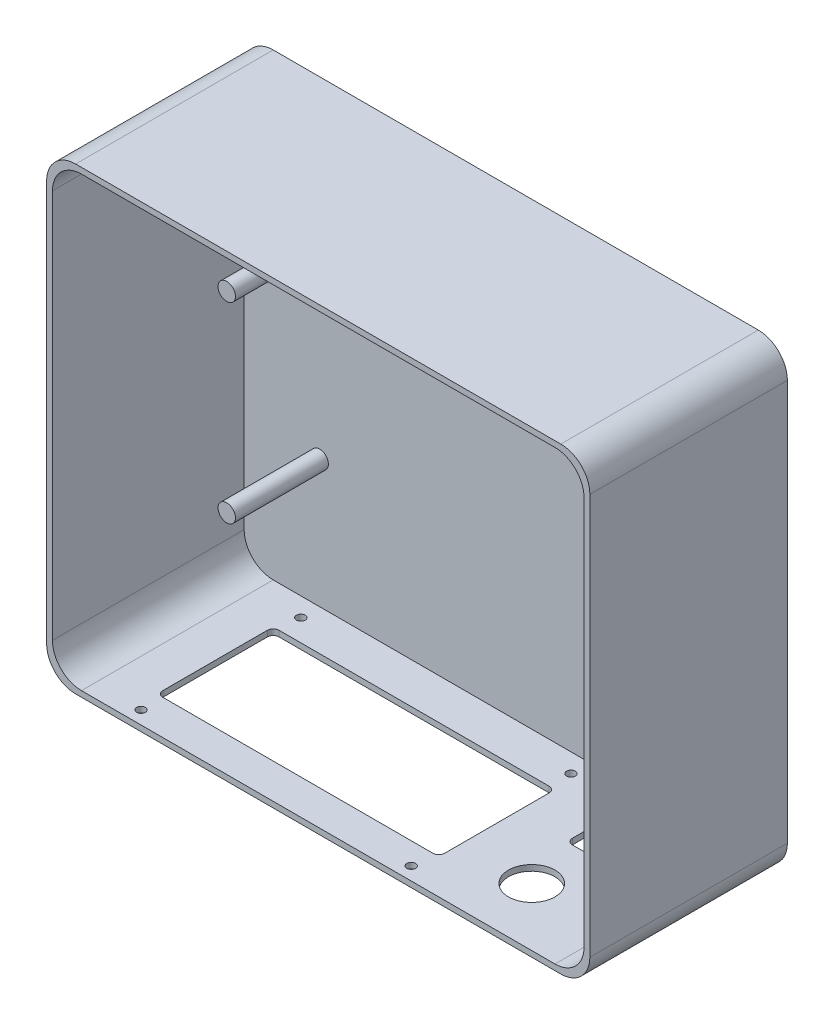
SolidWorks part; units mm, degrees
ref_plane "Front Plane" through (0, 0, 0) normal (0, 0, 1) x (1, 0, 0)
ref_plane "Top Plane" through (0, 0, 0) normal (0, 1, 0) x (1, 0, 0)
ref_plane "Right Plane" through (0, 0, 0) normal (1, 0, 0) x (0, 0, -1)
sketch "Sketch1" plane through (0, 0, 0) normal (0, 0, 1) x (1, 0, 0)
  line L1 (-93.5, 79) -> (93.5, 79)
  line L2 (-93.5, 79) -> (-93.5, -79)
  line L3 (-93.5, -79) -> (93.5, -79)
  line L4 (93.5, 79) -> (93.5, -79)
  line L5 (-93.5, 79) -> (93.5, -79) construction
  line L6 (-93.5, -79) -> (93.5, 79) construction
  line L7 (-91.5, 77) -> (91.5, 77)
  line L8 (-91.5, 77) -> (-91.5, -77)
  line L9 (-91.5, -77) -> (91.5, -77)
  line L10 (91.5, 77) -> (91.5, -77)
  line L11 (-91.5, 77) -> (91.5, -77) construction
  line L12 (-91.5, -77) -> (91.5, 77) construction
  point P0 (0, 0)
  point P6 (0, 0)
  dimension "D1" = 187
  dimension "D2" = 158
  dimension "D3" = 2
  dimension "D4" = 2
extrude "Boss-Extrude1" add sketch "Sketch1" along normal blind 66
sketch "Sketch2" plane through (0, 0, 0) normal (0, 0, -1) x (-1, 0, 0)
  line L1 (-93.5, 79) -> (93.5, 79)
  line L2 (-93.5, 79) -> (-93.5, -79)
  line L3 (-93.5, -79) -> (93.5, -79)
  line L4 (93.5, 79) -> (93.5, -79)
  line L5 (-93.5, 79) -> (93.5, -79) construction
  line L6 (-93.5, -79) -> (93.5, 79) construction
  point P0 (0, 0)
extrude "Boss-Extrude2" add sketch "Sketch2" along normal blind 2
fillet "Fillet1" radius 10 4 edges at (91.5, -77, 33) (91.5, 77, 33) (-91.5, -77, 33) (-91.5, 77, 33)
fillet "Fillet2" radius 10 4 edges at (93.5, -79, 32) (-93.5, -79, 32) (93.5, 79, 32) (-93.5, 79, 32)
sketch "Sketch3" plane through (0, 0, 0) normal (0, 0, 1) x (1, 0, 0)
  line L5 (-65.5, 33) -> (65.5, -33) construction
  line L6 (-65.5, -33) -> (65.5, 33) construction
  line L9 (62.5, -33) -> (65.5, -33)
  circle A0 centre (-65.5, 33) radius 3
  circle A1 centre (65.5, 33) radius 3
  circle A2 centre (65.5, -33) radius 3
  circle A3 centre (-65.5, -33) radius 3
  point P0 (0, 0)
  dimension "D3" = 6
  dimension "D4" = 6
  dimension "D5" = 6
  dimension "D6" = 6
  dimension "D1" = 66
  dimension "D2" = 131
extrude "Boss-Extrude3" add sketch "Sketch3" along normal blind 32
sketch "Sketch4" plane through (0, -79, 0) normal (0, -1, 0) x (1, 0, 0)
  line L0 (-93.5, -2) -> (-93.5, 66) construction
  line L1 (-67.5, 54) -> (29.5, 54)
  line L2 (-67.5, 54) -> (-67.5, 14)
  line L3 (-67.5, 14) -> (29.5, 14)
  line L4 (29.5, 54) -> (29.5, 14)
  line L5 (-67.5, 54) -> (29.5, 14) construction
  line L6 (-67.5, 14) -> (29.5, 54) construction
  line L7 (-83.5, 66) -> (83.5, 66) construction
  point P0 (-19, 34)
  dimension "D1" = 40
  dimension "D2" = 97
  dimension "D3" = 26
  dimension "D4" = 12
extrude "Cut-Extrude1" cut sketch "Sketch4" against normal blind 10
sketch "Sketch5" plane through (0, -79, 0) normal (0, -1, 0) x (1, 0, 0)
  line L0 (-19, 14) -> (-19, 54) construction
  line L1 (-67.5, 14) -> (29.5, 14) construction
  line L2 (29.5, 54) -> (-67.5, 54) construction
  line L3 (-19, 54) -> (-19, 34) construction
  line L4 (-19, 34) -> (29.5, 34) construction
  line L5 (29.5, 14) -> (29.5, 54) construction
  line L11 (-65.5, 61.5) -> (27.5, 6.5) construction
  line L12 (-65.5, 6.5) -> (27.5, 61.5) construction
  circle A0 centre (-65.5, 61.5) radius 1.5
  circle A1 centre (27.5, 61.5) radius 1.5
  circle A2 centre (-65.5, 6.5) radius 1.5
  circle A3 centre (27.5, 6.5) radius 1.5
  dimension "D3" = 3
  dimension "D4" = 3
  dimension "D5" = 3
  dimension "D6" = 3
  dimension "D1" = 93
  dimension "D2" = 55
extrude "Cut-Extrude2" cut sketch "Sketch5" against normal blind 10
sketch "Sketch6" plane through (0, -79, 0) normal (0, -1, 0) x (1, 0, 0)
  line L0 (53.5, 66) -> (53.5, -2) construction
  line L1 (-83.5, 66) -> (83.5, 66) construction
  line L2 (83.5, -2) -> (-83.5, -2) construction
  line L3 (93.5, 66) -> (93.5, -2) construction
  line L4 (47, 27.5) -> (60, 27.5)
  line L5 (47, 27.5) -> (47, 8.5)
  line L6 (47, 8.5) -> (60, 8.5)
  line L7 (60, 27.5) -> (60, 8.5)
  line L8 (47, 27.5) -> (60, 8.5) construction
  line L9 (47, 8.5) -> (60, 27.5) construction
  circle A0 centre (53.5, 46) radius 8
  point P8 (53.5, 18)
  dimension "D2" = 20
  dimension "D3" = 16
  dimension "D1" = 40
  dimension "D4" = 19
  dimension "D5" = 13
  dimension "D6" = 20
extrude "Cut-Extrude3" cut sketch "Sketch6" against normal blind 10
fillet "Fillet3" radius 2 8 edges at (47, -78, 27.5) (47, -78, 8.5) (60, -78, 8.5) (60, -78, 27.5) (-67.5, -78, 14) (-67.5, -78, 54) (29.5, -78, 54) (29.5, -78, 14)
